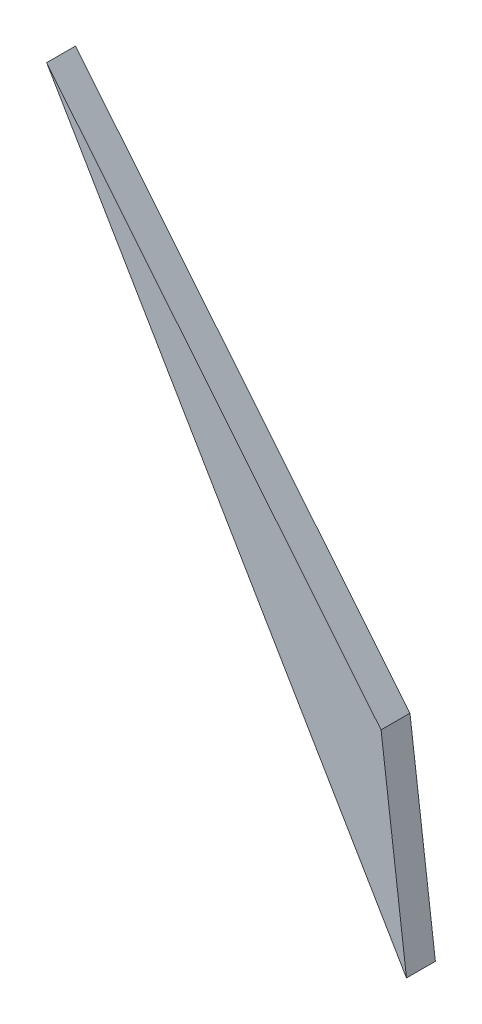
SolidWorks part; units mm, degrees
ref_plane "Plan de face" through (0, 0, 0) normal (0, 0, 1) x (1, 0, 0)
ref_plane "Plan de dessus" through (0, 0, 0) normal (0, 1, 0) x (1, 0, 0)
ref_plane "Plan de droite" through (0, 0, 0) normal (1, 0, 0) x (0, 0, -1)
sketch "Esquisse1" plane through (0, 0, 0) normal (0, 0, 1) x (1, 0, 0)
  line L0 (-2.8693, -1.2277) -> (-37.6043, 41.416)
  line L1 (-37.6043, 41.416) -> (-0.2297, -22.2277)
  line L3 (-0.2297, -22.2277) -> (-2.8693, -1.2277)
  line L4 (-2.326, -1.8946) -> (-35.7924, 39.1915) construction
  line L5 (-2.0612, -7.6564) -> (-2.9766, -0.3741) construction
  line L6 (-35.7924, 39.1915) -> (-64.2396, 74.1157) construction
  point P2 (0, 0)
  point P3 (0, -22.2498)
  point P7 (-19.0592, 18.6484)
  point P8 (0, 0)
  point P9 (0, 0)
  point P12 (-2.8693, -10.8837)
  point P13 (-10.545, -15.1219)
  point P14 (0, 0)
  point P15 (-8.417, -16.9427)
  point P16 (-42.2474, 40.2935)
  point P19 (-1.0915, -15.7739)
  dimension "D1" = 55
  dimension "D2" = 21
extrude "Boss.-Extru.1" add sketch "Esquisse1" along normal blind 3
